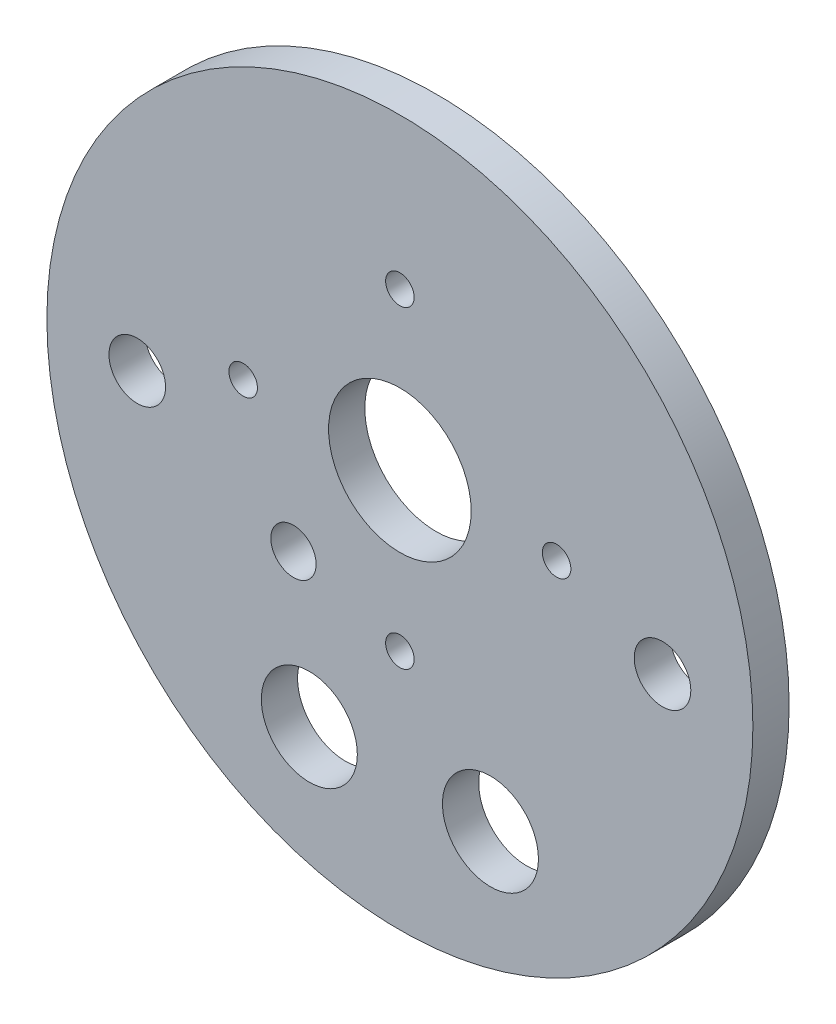
SolidWorks part; units mm, degrees
ref_plane "Front Plane" through (0, 0, 0) normal (0, 0, 1) x (1, 0, 0)
ref_plane "Top Plane" through (0, 0, 0) normal (0, 1, 0) x (1, 0, 0)
ref_plane "Right Plane" through (0, 0, 0) normal (1, 0, 0) x (0, 0, -1)
sketch "Sketch1" plane through (0, 0, 0) normal (0, 0, 1) x (1, 0, 0)
  circle A0 centre (0, 0) radius 49.5046
  dimension "D1" = 99.0092
extrude "Boss-Extrude1" add sketch "Sketch1" along normal blind 5.08
sketch "Sketch2" plane through (0, 0, 5.08) normal (0, 0, 1) x (1, 0, 0)
  circle A0 centre (0, 0) radius 47.625
  dimension "D1" = 95.25
extrude "Boss-Extrude2" add sketch "Sketch2" along normal blind 3.175
sketch "Sketch3" plane through (0, 0, 8.255) normal (0, 0, 1) x (1, 0, 0)
  line L0 (-21.9769, 6.35) -> (0, -15.6269) construction
  line L1 (-21.9769, 6.35) -> (0, 28.3269) construction
  line L2 (0, -15.6269) -> (21.9769, 6.35) construction
  line L3 (0, 28.3269) -> (21.9769, 6.35) construction
  circle A0 centre (-12.7, -31.1668) radius 6.731
  circle A1 centre (12.7, -31.1668) radius 6.731
  circle A2 centre (-12.7, -31.1668) radius 12.7 construction
  circle A3 centre (12.7, -31.1668) radius 12.7 construction
  circle A4 centre (12.7, -31.1668) radius 13.97 construction
  circle A5 centre (-12.7, -31.1668) radius 13.97 construction
  circle A6 centre (0, 0) radius 47.625 construction
  circle A7 centre (-36.83, 0) radius 3.9687
  circle A8 centre (36.83, 0) radius 3.9687
  circle A9 centre (0, 6.35) radius 15.24 construction
  circle A10 centre (-14.9213, -10.9686) radius 8.89 construction
  circle A11 centre (0, 6.35) radius 16.51 construction
  circle A12 centre (-14.9213, -10.9686) radius 7.62 construction
  circle A13 centre (0, 6.35) radius 10
  circle A14 centre (-14.9213, -10.9686) radius 3.175
  circle A15 centre (0, 28.3269) radius 2
  circle A16 centre (21.9769, 6.35) radius 2
  circle A17 centre (0, -15.6269) radius 2
  circle A18 centre (-21.9769, 6.35) radius 2
  circle A19 centre (0, 6.35) radius 31.55 construction
  dimension "D1" = 13.462
  dimension "D2" = 13.462
  dimension "D3" = 27.94
  dimension "D4" = 27.94
  dimension "D5" = 25.4
  dimension "D6" = 25.4
  dimension "D7" = 7.9375
  dimension "D8" = 7.9375
  dimension "D11" = 30.48
  dimension "D12" = 33.02
  dimension "D13" = 15.24
  dimension "D14" = 17.78
  dimension "D15" = 20
  dimension "D16" = 6.35
  dimension "D18" = 4
  dimension "D23" = 63.1
  dimension "D9" = 73.66
  dimension "D10" = 36.83
  dimension "D17" = 6.35
  dimension "D19" = 31.08
  dimension "D20" = 31.08
  dimension "D21" = 31.08
extrude "Cut-Extrude1" cut sketch "Sketch3" against normal through all
sketch "Sketch4" [suppressed] plane through (0, 0, 6.35) normal (0, 0, 1) x (1, 0, 0)
  circle A0 centre (0, 0) radius 49.5046
  circle A1 centre (0, 0) radius 47.6885
extrude "Boss-Extrude3" [suppressed] add sketch "Sketch4" against normal up to surface (3.175 mm away)
sketch "Sketch5" [suppressed] plane through (0, 0, 6.35) normal (0, 0, 1) x (1, 0, 0)
  circle A0 centre (0, 6.35) radius 11.1125
extrude "Boss-Extrude4" [suppressed] add sketch "Sketch5" against normal up to surface (6.35 mm away)
sketch "Sketch6" [suppressed] plane through (0, 0, 6.35) normal (0, 0, 1) x (1, 0, 0)
  circle A0 centre (-23.622, -17.272) radius 2.54
  circle A1 centre (23.622, -17.272) radius 2.54
extrude "Boss-Extrude5" [suppressed] add sketch "Sketch6" against normal blind 6.35
sketch "Sketch7" plane through (0, 0, 8.255) normal (0, 0, 1) x (1, 0, 0)
  circle A0 centre (0, 0) radius 56.4231
extrude "Cut-Extrude2" cut sketch "Sketch7" against normal blind 3.175
